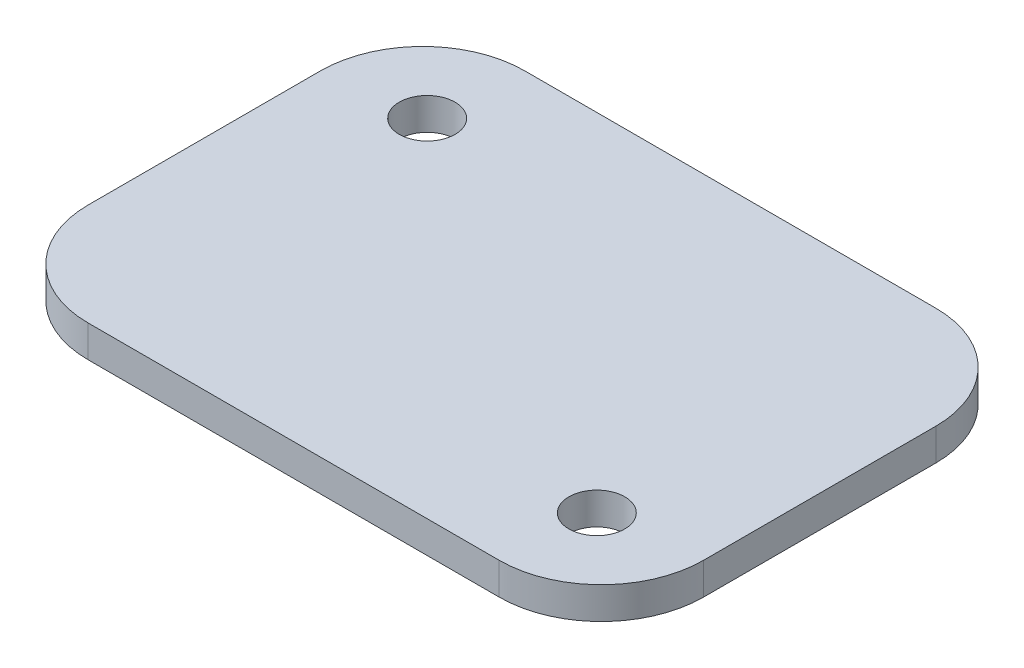
SolidWorks part; units mm, degrees
ref_plane "Front Plane" through (0, 0, 0) normal (0, 0, 1) x (1, 0, 0)
ref_plane "Top Plane" through (0, 0, 0) normal (0, 1, 0) x (1, 0, 0)
ref_plane "Right Plane" through (0, 0, 0) normal (1, 0, 0) x (0, 0, -1)
sketch "Sketch1" plane through (0, 0, 0) normal (0, 1, 0) x (1, 0, 0)
  line L1 (-20.447, -21.717) -> (20.447, -21.717)
  line L2 (-30.607, -11.557) -> (-30.607, 11.557)
  line L3 (-20.447, 21.717) -> (20.447, 21.717)
  line L4 (30.607, -11.557) -> (30.607, 11.557)
  line L5 (-30.607, -21.717) -> (30.607, 21.717) construction
  line L6 (-30.607, 21.717) -> (30.607, -21.717) construction
  arc A0 (30.607, -11.557) -> (20.447, -21.717) centre (20.447, -11.557) cw
  arc A1 (-20.447, -21.717) -> (-30.607, -11.557) centre (-20.447, -11.557) cw
  arc A2 (-30.607, 11.557) -> (-20.447, 21.717) centre (-20.447, 11.557) cw
  arc A3 (30.607, 11.557) -> (20.447, 21.717) centre (20.447, 11.557) ccw
  point P0 (0, 0)
  dimension "D3" = 10.16
  dimension "D1" = 61.214
  dimension "D2" = 43.434
extrude "Boss-Extrude1" add sketch "Sketch1" along normal blind 3.175
hole_wizard "7/32 (0.21875) Diameter Hole1" positions "Sketch2" profile "Sketch3" hole size "7/32" standard "ANSI Inch" end condition through all
sketch "Sketch2" plane through (0, 3.175, 0) normal (0, 1, 0) x (1, 0, 0)
  line L5 (-21.2145, 12.7769) -> (21.2145, -12.7769)
  line L8 (-20.447, -21.717) -> (20.447, -21.717) construction
  point P0 (-21.2145, 12.7769)
  point P2 (21.2145, -12.7769)
  dimension "D1" = 31.059
  dimension "D2" = 49.53
sketch "Sketch3" plane through (-21.2145, 3.175, -12.7769) normal (1, 0, 0) x (0, 0, 1)
  line L0 (0, 0) -> (0, 3.175)
  line L1 (0, 3.175) -> (2.7781, 3.175)
  line L2 (2.7781, 3.175) -> (2.7781, 0)
  line L5 (2.7781, 0) -> (0, 0)
  line L11 (0, -6.35) -> (0, 107.95) construction
  dimension "Thru Hole Dia." = 5.5562
  dimension "Thru Hole Depth" = 3.175
